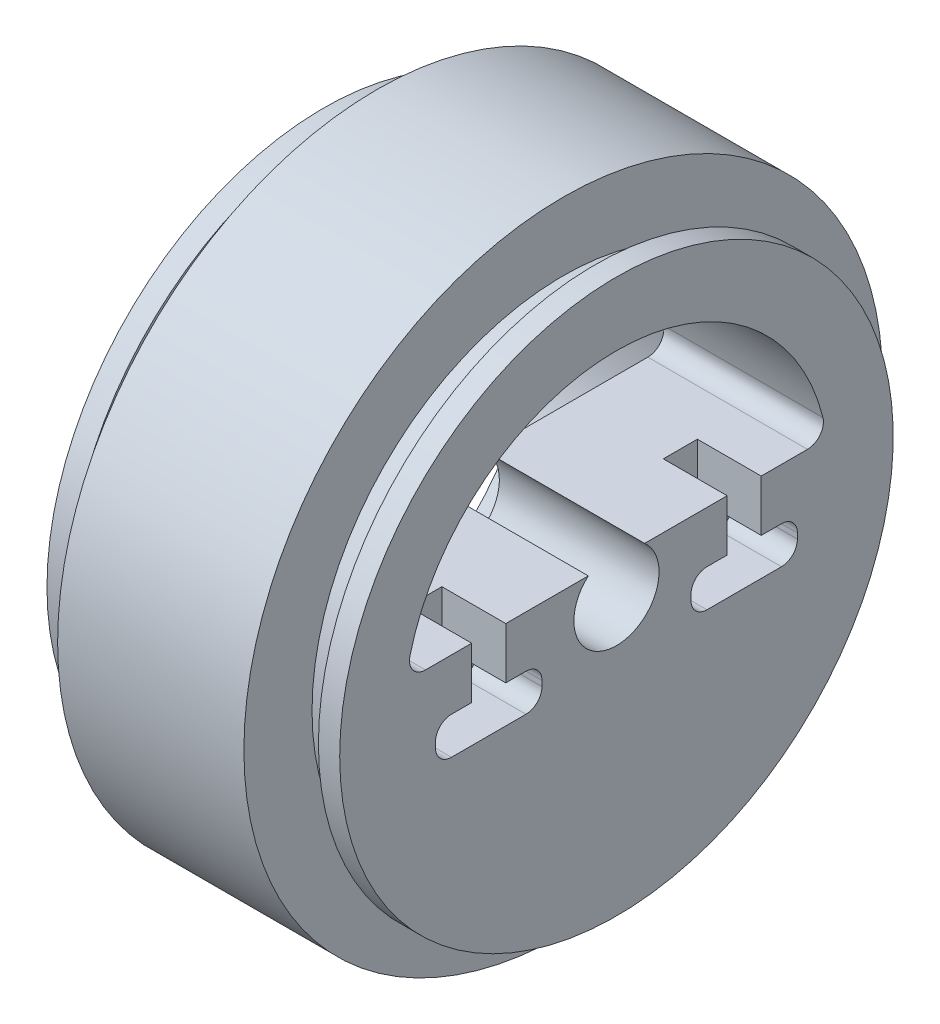
SolidWorks part; units mm, degrees
ref_plane "Plan de face" through (0, 0, 0) normal (0, 0, 1) x (1, 0, 0)
ref_plane "Plan de dessus" through (0, 0, 0) normal (0, 1, 0) x (1, 0, 0)
ref_plane "Plan de droite" through (0, 0, 0) normal (1, 0, 0) x (0, 0, -1)
sketch "Esquisse1" plane through (0, 0, 0) normal (0, 0, 1) x (1, 0, 0)
  line L0 (-9.1324, 20) -> (-9.1324, 26)
  line L1 (-4.1324, 30) -> (13.3676, 30)
  line L2 (-7.1324, 23.6) -> (-4.1324, 23.6)
  line L3 (0, 23.6) -> (13.3676, 23.6) construction
  line L4 (-7.1324, 23.6) -> (-7.1324, 26)
  line L5 (18.3676, 26) -> (16.3676, 26)
  line L6 (3.3676, 20) -> (-9.1324, 20)
  line L7 (-9.1324, 26) -> (-7.1324, 26)
  line L8 (16.3676, 23.6) -> (16.3676, 26)
  line L9 (16.3676, 23.6) -> (13.3676, 23.6)
  line L10 (-9.1324, -1.9975) -> (-9.1324, 33.1761) construction
  line L11 (-7.1324, -1.9975) -> (-7.1324, 33.1761) construction
  line L12 (13.3676, 23.6) -> (13.3676, 30)
  line L13 (0, 30) -> (13.3676, 30) construction
  line L14 (-4.1324, 23.6) -> (-4.1324, 30)
  line L15 (3.3676, 4) -> (3.3676, 20)
  line L16 (18.3676, 4) -> (18.3676, 26)
  line L17 (3.3676, 0) -> (26.9465, 0) construction
  line L18 (3.3676, -1.9975) -> (3.3676, 26) construction
  line L19 (18.3676, -1.9975) -> (18.3676, 26) construction
  line L20 (3.3676, 4) -> (18.3676, 4)
  line L23 (3.3676, 4) -> (26.9465, 4) construction
  dimension "D2" = 16
  dimension "D3" = 6
  dimension "D4" = 12.5
  dimension "D5" = 15
  dimension "D6" = 2
  dimension "D7" = 2.4
  dimension "D8" = 3
  dimension "D9" = 6.4
  dimension "D10" = 17.5
  dimension "D11" = 6.4
  dimension "D12" = 3
  dimension "D13" = 2.4
  dimension "D14" = 2
  dimension "D15" = 22
  dimension "D16" = 4
revolve "Révolution1" add sketch "Esquisse1" angle 360 about L17
sketch "Esquisse2" plane through (18.3676, 0, 0) normal (1, 0, 0) x (0, 0, -1)
  line L1 (17.9444, 3) -> (-17.9444, 3)
  arc A0 (-17.9444, 3) -> (-19.3993, 4.8649) centre (-17.9444, 4.5) cw
  arc A1 (19.3993, 4.8649) -> (-19.3993, 4.8649) centre (0, 0) ccw
  arc A2 (17.9444, 3) -> (19.3993, 4.8649) centre (17.9444, 4.5) ccw
  dimension "D1" = 1.5
extrude "Extrusion1" cut sketch "Esquisse2" against normal through all
sketch "Esquisse3" plane through (18.3676, 0, 0) normal (1, 0, 0) x (0, 0, -1)
  line L0 (-10.4, -1.8292) -> (-10.4, 3.1708)
  line L1 (-13.6, -1.8292) -> (-15.5, -1.8292)
  line L2 (-13.6, -1.8292) -> (-13.6, 3.1708)
  line L3 (-10.4, 3.1708) -> (-13.6, 3.1708)
  line L4 (-8.5, -1.8292) -> (-10.4, -1.8292)
  line L5 (-7, -1.8292) -> (-17, -1.8292) construction
  line L6 (-7, -5.3292) -> (-17, -5.3292) construction
  line L7 (0, 0) -> (0, 7.585) construction
  line L8 (-10.4, -1.8292) -> (-13.6, -1.8292) construction
  line L9 (-8.5, -5.3292) -> (-15.5, -5.3292)
  line L10 (-17, -3.3292) -> (-17, -3.8292)
  line L11 (-7, -3.3292) -> (-7, -3.8292)
  line L12 (7, -3.3292) -> (7, -3.8292)
  line L13 (17, -3.3292) -> (17, -3.8292)
  line L14 (8.5, -5.3292) -> (15.5, -5.3292)
  line L15 (8.5, -1.8292) -> (10.4, -1.8292)
  line L16 (10.4, 3.1708) -> (13.6, 3.1708)
  line L17 (13.6, -1.8292) -> (13.6, 3.1708)
  line L18 (13.6, -1.8292) -> (15.5, -1.8292)
  line L19 (10.4, -1.8292) -> (10.4, 3.1708)
  arc A0 (-15.5, -1.8292) -> (-17, -3.3292) centre (-15.5, -3.3292) ccw
  arc A1 (-15.5, -5.3292) -> (-17, -3.8292) centre (-15.5, -3.8292) cw
  arc A2 (-8.5, -5.3292) -> (-7, -3.8292) centre (-8.5, -3.8292) ccw
  arc A3 (-8.5, -1.8292) -> (-7, -3.3292) centre (-8.5, -3.3292) cw
  arc A4 (8.5, -1.8292) -> (7, -3.3292) centre (8.5, -3.3292) ccw
  arc A5 (8.5, -5.3292) -> (7, -3.8292) centre (8.5, -3.8292) cw
  arc A6 (15.5, -5.3292) -> (17, -3.8292) centre (15.5, -3.8292) ccw
  arc A7 (15.5, -1.8292) -> (17, -3.3292) centre (15.5, -3.3292) cw
  dimension "D1" = 1.5
extrude "Extrusion2" cut sketch "Esquisse3" against normal blind 6
